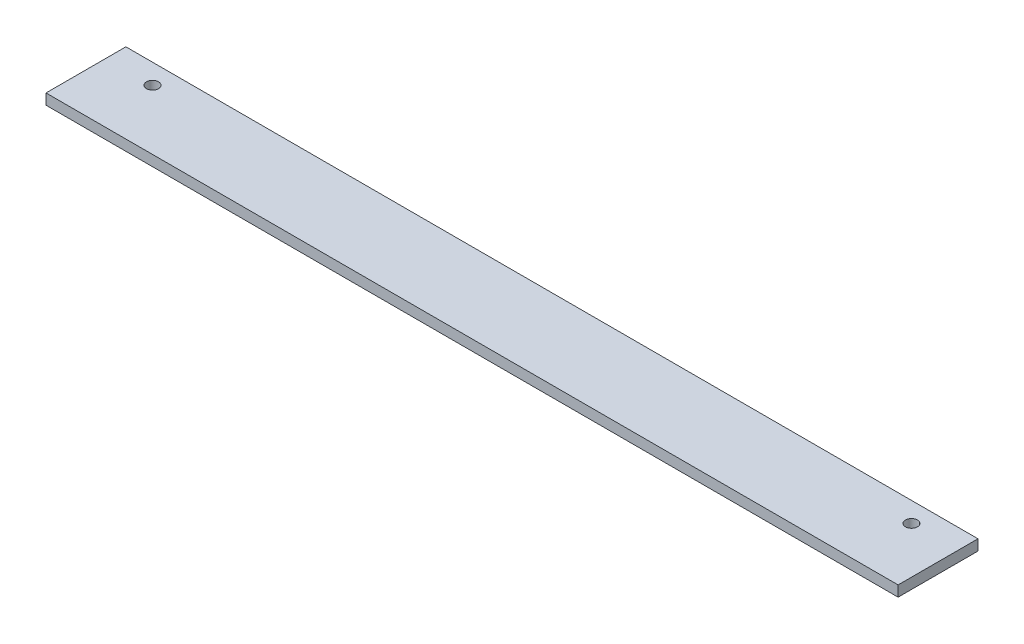
SolidWorks part; units mm, degrees
ref_plane "Спереди" through (0, 0, 0) normal (0, 0, 1) x (1, 0, 0)
ref_plane "Сверху" through (0, 0, 0) normal (0, 1, 0) x (1, 0, 0)
ref_plane "Справа" through (0, 0, 0) normal (1, 0, 0) x (0, 0, -1)
sketch "Эскиз1" plane through (0, 0, 0) normal (1, 0, 0) x (0, 0, -1)
  line L1 (-15, -2) -> (15, -2)
  line L2 (-15, -2) -> (-15, 2)
  line L3 (-15, 2) -> (15, 2)
  line L4 (15, -2) -> (15, 2)
  line L5 (-15, -2) -> (15, 2) construction
  line L6 (-15, 2) -> (15, -2) construction
  point P0 (0, 0)
  dimension "D1" = 4
  dimension "D2" = 30
extrude "Бобышка-Вытянуть1" add sketch "Эскиз1" along normal blind 320
sketch "Эскиз2" plane through (0, 2, 0) normal (0, 1, 0) x (1, 0, 0)
  line L0 (0, 15) -> (0, -15) construction
  line L1 (320, 15) -> (0, 15) construction
  line L2 (320, 15) -> (320, -15) construction
  circle A0 centre (17.5, 7.5) radius 2.25
  circle A1 centre (302.5, 7.5) radius 2.25
  dimension "D1" = 4.5
  dimension "D2" = 17.5
  dimension "D3" = 7.5
  dimension "D4" = 4.5
  dimension "D5" = 17.5
  dimension "D6" = 7.5
extrude "Вырез-Вытянуть1" cut sketch "Эскиз2" against normal through all
